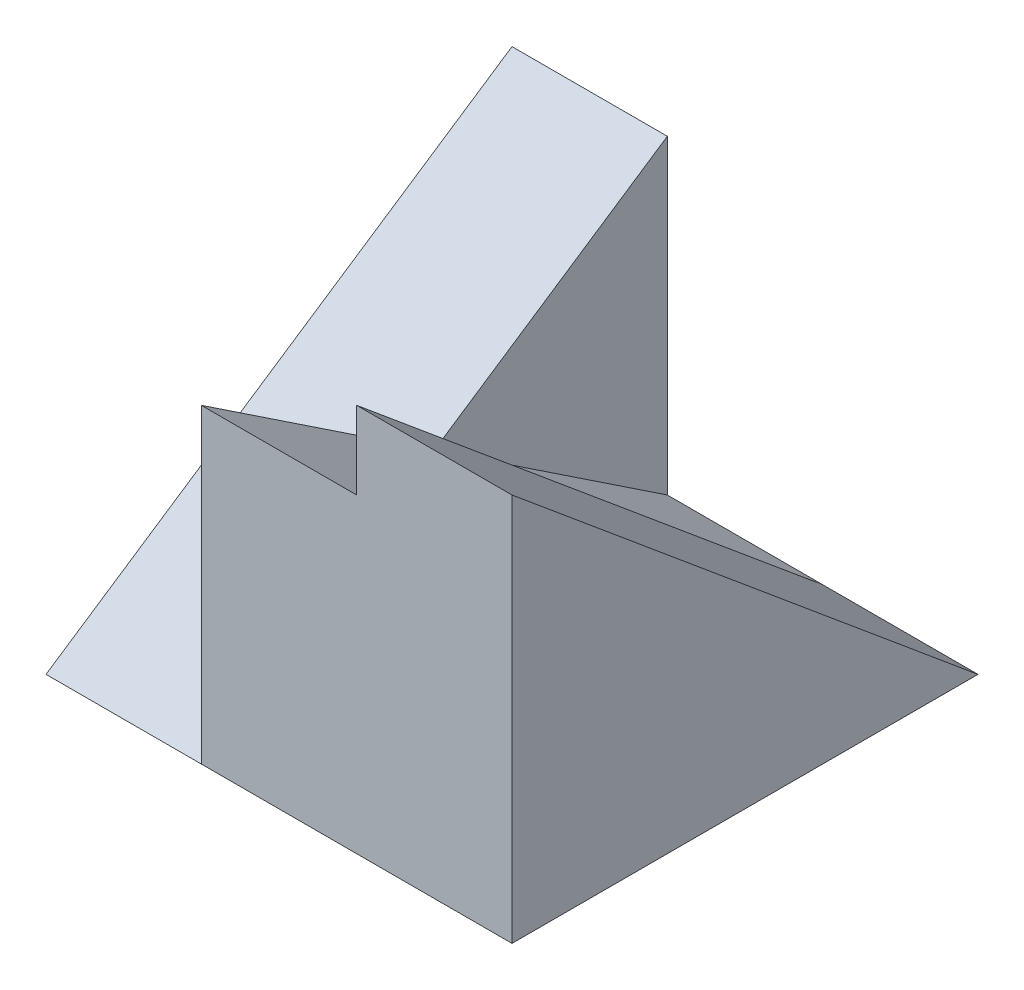
SolidWorks part; units mm, degrees
ref_plane "Front" through (0, 0, 0) normal (0, 0, 1) x (1, 0, 0)
ref_plane "Top" through (0, 0, 0) normal (0, 1, 0) x (1, 0, 0)
ref_plane "Right" through (0, 0, 0) normal (1, 0, 0) x (0, 0, -1)
sketch "Sketch1" plane through (0, 0, 0) normal (0, 1, 0) x (1, 0, 0)
  line L1 (-3, -3) -> (3, -3)
  line L2 (-3, -3) -> (-3, 3)
  line L3 (-3, 3) -> (3, 3)
  line L4 (3, -3) -> (3, 3)
  line L5 (-3, -3) -> (3, 3) construction
  line L6 (-3, 3) -> (3, -3) construction
  point P0 (0, 0)
  dimension "D1" = 6
  dimension "D2" = 6
extrude "Boss-Extrude1" add sketch "Sketch1" along normal blind 5
sketch "Sketch2" plane through (-3, 0, 0) normal (-1, 0, 0) x (0, 0, 1)
  line L1 (-3, 5) -> (-3, 4)
  line L4 (-3, 0) -> (3, 0)
  line L5 (3, 0) -> (3, 5)
  line L6 (3, 5) -> (-3, 5)
  line L7 (-3, 5) -> (-3, 0)
  line L10 (3, 5) -> (-3, 5)
  line L14 (-3, 5) -> (-3, 0) construction
  line L15 (-3, 4) -> (3, 0)
  line L16 (3, 0) -> (3, 5)
  dimension "D2" = 1
  dimension "D1" = 0
extrude "Cut-Extrude1" cut sketch "Sketch2" against normal blind 2
sketch "Sketch3" plane through (-1, 0, 0) normal (-1, 0, 0) x (0, 0, 1)
  line L0 (-3, 0) -> (3, 4)
  line L1 (3, 4) -> (3, 0)
  line L3 (3, 5) -> (-3, 5)
  line L4 (-3, 5) -> (-3, 4)
  line L5 (3, 0) -> (3, 5)
  line L6 (3, 5) -> (-3, 5)
  line L8 (3, 0) -> (3, 5)
  line L10 (-3, 0) -> (3, 0)
  line L11 (-3, 0) -> (3, 0)
  line L12 (-3, 4) -> (-3, 0)
  line L13 (3, 0) -> (-3, 4)
  line L14 (3, 0) -> (-3, 4)
  line L16 (-3, 4) -> (-3, 0)
  line L19 (-3, 5) -> (-3, 4)
  line L20 (-3, 4) -> (3, 0)
  line L21 (-3, 4) -> (3, 0)
  dimension "D3" = 4
  dimension "D4" = 1
  dimension "D5" = 4
  dimension "D1" = 0
  dimension "D2" = 0
extrude "Cut-Extrude2" cut sketch "Sketch3" against normal blind 2
sketch "Sketch4" plane through (1, 0, 0) normal (-1, 0, 0) x (0, 0, 1)
  line L0 (3, 5) -> (-3, 0)
  line L4 (3, 4) -> (3, 5)
  line L5 (3, 5) -> (-3, 5)
  line L6 (-3, 5) -> (-3, 0)
  line L7 (-3, 0) -> (3, 4)
  line L9 (3, 5) -> (-3, 5)
  line L10 (-3, 5) -> (-3, 0)
  line L13 (-3, 0) -> (3, 4)
  dimension "D1" = 0
extrude "Cut-Extrude3" cut sketch "Sketch4" against normal blind 2
